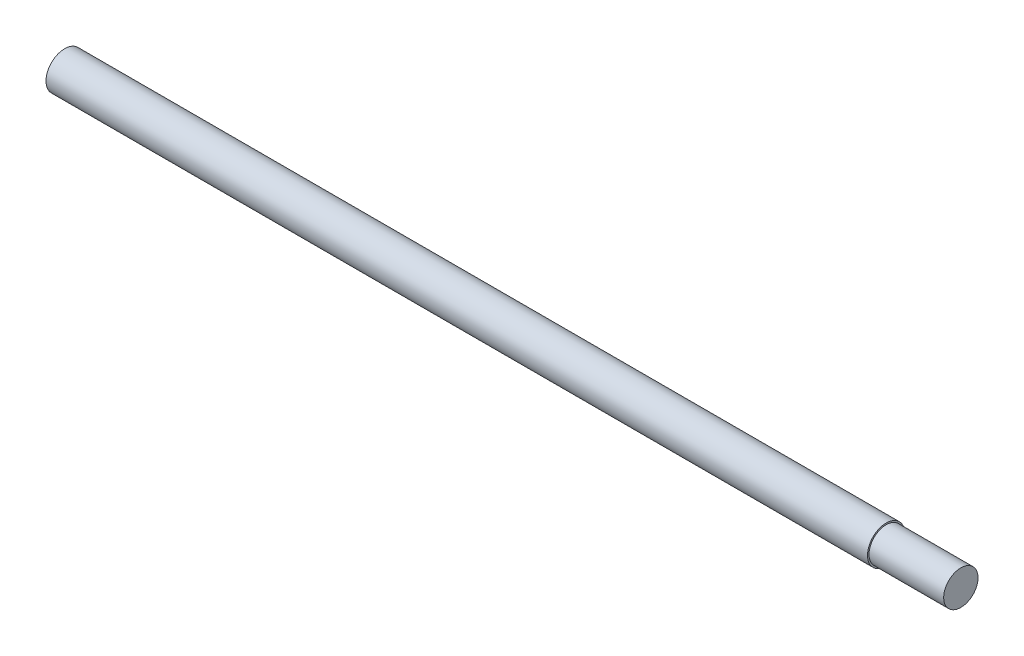
SolidWorks part; units mm, degrees
ref_plane "Front Plane" through (0, 0, 0) normal (0, 0, 1) x (1, 0, 0)
ref_plane "Top Plane" through (0, 0, 0) normal (0, 1, 0) x (1, 0, 0)
ref_plane "Right Plane" through (0, 0, 0) normal (1, 0, 0) x (0, 0, -1)
sketch "Sketch1" plane through (0, 0, 0) normal (0, 1, 0) x (1, 0, 0)
  line L1 (57.4357, -3.6559) -> (57.4357, -5.9559)
  line L2 (57.4357, -5.9559) -> (47.4357, -5.9559)
  line L3 (47.4357, -5.9559) -> (47.4357, -6.1559)
  line L4 (47.4357, -6.1559) -> (-62.5643, -6.1559)
  line L5 (-62.5643, -6.1559) -> (-62.5643, -3.6559)
  line L6 (-62.5643, -3.6559) -> (57.4357, -3.6559)
  dimension "D1" = 2.5
  dimension "D2" = 2.3
  dimension "D3" = 110
  dimension "D4" = 120
revolve "Revolve1" add sketch "Sketch1" angle 360 about L6
